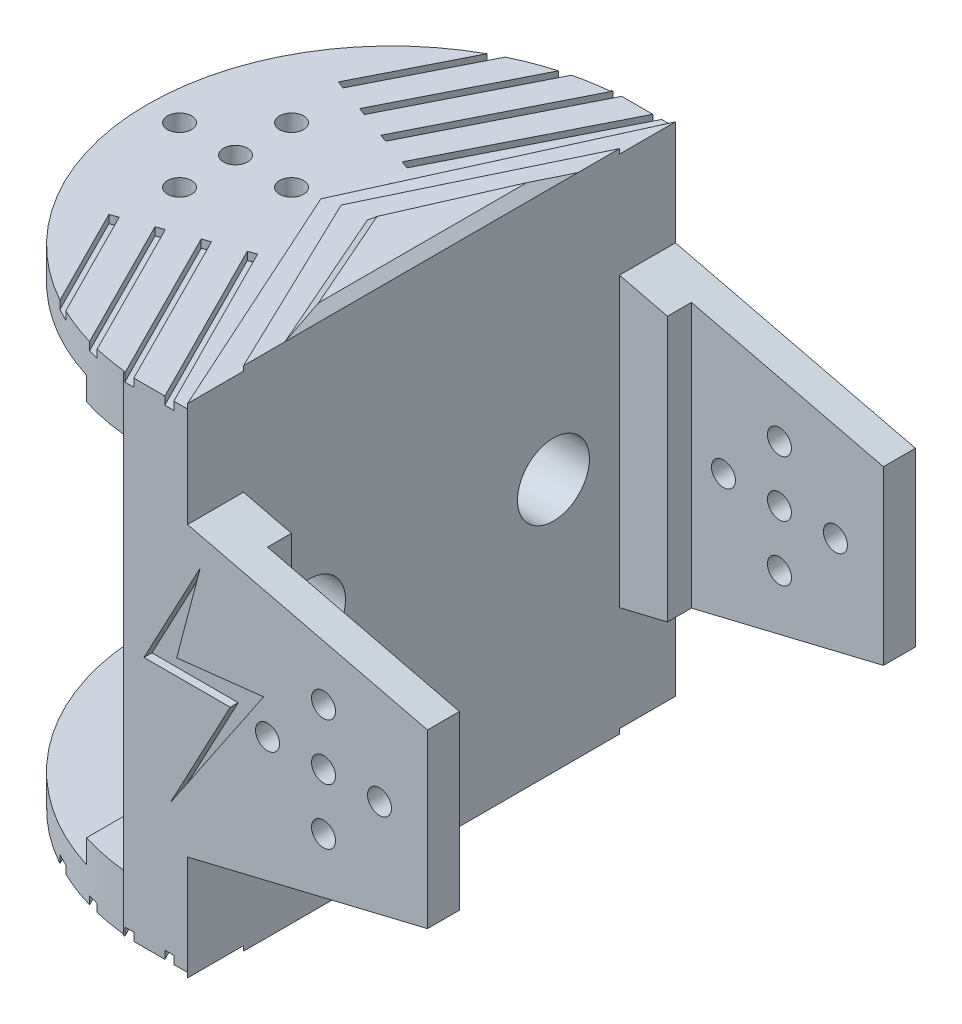
SolidWorks part; units mm, degrees
ref_plane "Front" through (0, 0, 0) normal (0, 0, 1) x (1, 0, 0)
ref_plane "Top" through (0, 0, 0) normal (0, 1, 0) x (1, 0, 0)
ref_plane "Right" through (0, 0, 0) normal (1, 0, 0) x (0, 0, -1)
sketch "草图1" plane through (0, 0, 0) normal (0, 1, 0) x (1, 0, 0)
  line L0 (50.6168, 0) -> (43.6168, 0) construction
  line L1 (43.6168, -30.5) -> (50.6168, -30.5)
  line L3 (43.6168, 30.5) -> (50.6168, 30.5)
  line L4 (50.6168, -30.5) -> (50.6168, 30.5)
  line L5 (-50.6168, -30.5) -> (50.6168, 30.5) construction
  line L6 (-50.6168, 30.5) -> (50.6168, -30.5) construction
  arc A1 (43.6168, 30.5) -> (43.6168, -30.5) centre (43.6168, 0) ccw
  point P0 (0, 0)
extrude "凸台-拉伸1" add sketch "草图1" along normal blind 61
sketch "草图2" plane through (0, 0, 30.5) normal (0, 0, 1) x (1, 0, 0)
  line L0 (50.6168, 61) -> (50.6168, 57) construction
  line L1 (50.6168, 61) -> (50.6168, 0) construction
  line L2 (50.6168, 57) -> (46.6168, 57) construction
  line L3 (50.6168, 0) -> (50.6168, 4) construction
  line L4 (50.6168, 4) -> (46.6168, 4) construction
  line L5 (46.6168, 57) -> (46.6168, 4)
  line L6 (46.6168, 4) -> (6.6168, 4)
  line L7 (6.6168, 4) -> (6.6168, 57)
  line L8 (6.6168, 57) -> (46.6168, 57)
extrude "切除-拉伸1" cut sketch "草图2" against normal blind 61
sketch "草图3" plane through (0, 61, 0) normal (0, 1, 0) x (1, 0, 0)
  circle A1 centre (24.1168, 0) radius 4
extrude "切除-拉伸2" cut sketch "草图3" against normal blind 61
sketch "草图6" plane through (46.6168, 0, 0) normal (-1, 0, 0) x (0, 0, 1)
  line L0 (-30.5, 61) -> (-30.5, 0)
  line L1 (-30.5, 0) -> (30.5, 0)
  line L2 (30.5, 0) -> (30.5, 61)
  line L3 (30.5, 61) -> (-30.5, 61)
extrude "凸台-拉伸3" add sketch "草图6" along normal blind 6
sketch "草图7" plane through (0, 57, 0) normal (0, -1, 0) x (1, 0, 0)
  line L0 (40.6168, 30.3521) -> (40.6168, -30.3521)
  arc A0 (40.6168, 30.3521) -> (40.6168, -30.3521) centre (43.6168, 0) ccw
extrude "凸台-拉伸4" add sketch "草图7" along normal blind 6
sketch "草图8" plane through (0, 51, 0) normal (0, -1, 0) x (1, 0, 0)
  line L0 (40.6168, -30.3521) -> (34.6168, -30.3521) construction
  line L1 (9.6904, -10) -> (9.6904, 10)
  line L2 (34.6168, -30.3521) -> (24.1168, -25.2271)
  line L4 (24.1168, -25.2271) -> (9.6904, -10)
  line L6 (24.1168, 30.2691) -> (9.6904, 10)
  line L7 (34.6168, -30.3521) -> (34.6168, 33.6388)
  line L8 (34.6168, 33.6388) -> (24.1168, 30.2691)
extrude "切除-拉伸4" cut sketch "草图8" against normal blind 6
sketch "草图21" plane through (0, 61, 0) normal (0, 1, 0) x (1, 0, 0)
  circle A0 centre (24.1168, 0) radius 4
  circle A1 centre (24.1168, 0) radius 1.5
extrude "凸台-拉伸10" add sketch "草图21" against normal blind 4
sketch "草图22" plane through (0, 61, 0) normal (0, 1, 0) x (1, 0, 0)
  line L0 (24.1168, 0) -> (31.1168, 0) construction
  circle A0 centre (31.1168, 0) radius 1.5
  circle A1 centre (24.1168, -7) radius 1.5
  circle A2 centre (17.1168, 0) radius 1.5
  circle A3 centre (24.1168, 7) radius 1.5
  point P14 (24.1168, 0)
  dimension "D1" = 4
extrude "切除-拉伸11" cut sketch "草图22" against normal blind 4
sketch "草图23" plane through (50.6168, 0, 0) normal (1, 0, 0) x (0, 0, -1)
  line L0 (-30.5, 61) -> (-30.5, 0)
  line L1 (-30.5, 0) -> (30.5, 0)
  line L2 (30.5, 0) -> (30.5, 61)
  line L3 (30.5, 61) -> (-30.5, 61)
extrude "切除-拉伸12" cut sketch "草图23" against normal blind 2
sketch "草图24" plane through (0, 0, 30.5) normal (0, 0, 1) x (1, 0, 0)
  line L0 (40.6168, 51) -> (40.6168, 54.1)
  line L1 (40.6168, 0) -> (40.6168, 61) construction
  line L2 (40.6168, 54.1) -> (21.6591, 54.1)
  line L3 (21.6591, 54.1) -> (21.6591, 51)
  line L4 (21.6591, 51) -> (40.6168, 51)
  line L5 (40.6168, 30.5) -> (24.5889, 30.5) construction
extrude "切除-拉伸13" cut sketch "草图24" against normal blind 103 and the other way blind 38
ref_plane "基准面1" through (0, 30.5, 0) normal (0, -1, 0) x (-1, 0, 0)
mirror "镜向1" about plane through (0, 30.5, 0) normal (0, -1, 0) of "切除-拉伸4", "凸台-拉伸4", "切除-拉伸11", "切除-拉伸13"
sketch "草图25" plane through (0, 0, 0) normal (0, -1, 0) x (1, 0, 0)
  circle A0 centre (24.1168, 0) radius 4
  circle A1 centre (24.1168, 0) radius 1.5
extrude "凸台-拉伸11" add sketch "草图25" against normal blind 4
sketch "草图26" plane through (0, 0, 30.5) normal (0, 0, 1) x (1, 0, 0)
  line L0 (48.6168, 12.5) -> (48.6168, 48.5)
  line L1 (48.6168, 61) -> (48.6168, 0) construction
  line L2 (48.6168, 30.5) -> (78.6168, 30.5) construction
  line L3 (78.6168, 19.7437) -> (78.6168, 41.2563)
  line L4 (48.6168, 48.5) -> (78.6168, 41.2563)
  line L5 (48.6168, 12.5) -> (78.6168, 19.7437)
  line L6 (48.6168, 30.5) -> (65.6168, 30.5) construction
  line L7 (65.6168, 30.5) -> (65.6168, 37.5)
  circle A0 centre (65.6168, 30.5) radius 1.5
  circle A1 centre (65.6168, 37.5) radius 1.5
  circle A2 centre (72.6168, 30.5) radius 1.5
  circle A3 centre (65.6168, 23.5) radius 1.5
  circle A4 centre (58.6168, 30.5) radius 1.5
  point P21 (65.6168, 30.5)
ref_plane "基准面2" through (0, 0, 0) normal (0, 0, 1) x (1, 0, 0)
extrude "凸台-拉伸12" add sketch "草图26" against normal blind 7
sketch "草图27" plane through (0, 0, 23.5) normal (0, 0, -1) x (-1, 0, 0)
  line L0 (-48.6168, 48.5) -> (-54.6168, 48.5) construction
  line L1 (-65.6168, 49.1559) -> (-88.6288, 40.6)
  line L2 (-88.6288, 40.6) -> (-88.6288, 5.4717)
  line L3 (-88.6288, 5.4717) -> (-65.6168, 5.4717)
  line L4 (-55.5168, 53.0968) -> (-54.6168, 48.5)
  line L6 (-55.5168, 53.0968) -> (-65.6168, 49.1559)
  line L8 (-55.5168, 5.4717) -> (-65.6168, 5.4717)
  line L9 (-54.6168, 48.5) -> (-54.6168, 7.907)
  line L10 (-54.6168, 7.907) -> (-55.5168, 5.4717)
extrude "切除-拉伸14" cut sketch "草图27" against normal blind 3
mirror "镜向2" about plane through (0, 0, 0) normal (0, 0, 1) of "切除-拉伸14", "凸台-拉伸12"
sketch "草图30" plane through (48.6168, 0, 0) normal (1, 0, 0) x (0, 0, -1)
  line L0 (0, 61) -> (0, 0) construction
  line L1 (30.5, 61) -> (-30.5, 61) construction
  line L2 (0, 0) -> (-30.5, 30.5) construction
  line L3 (-30.5, 19.7437) -> (-30.5, 41.2563) construction
  line L4 (-30.5, 30.5) -> (0, 30.5) construction
  line L6 (0, 30.5) -> (30.5, 30.5) construction
  line L7 (30.5, 19.7437) -> (30.5, 41.2563) construction
  circle A0 centre (-15.25, 30.5) radius 4.5
  circle A1 centre (15.25, 30.5) radius 4.5
extrude "切除-拉伸15" cut sketch "草图30" against normal blind 46
sketch "草图31" plane through (0, 61, 0) normal (0, 1, 0) x (1, 0, 0)
  line L0 (48.6168, 30.5) -> (34.7866, 0)
  line L1 (34.7866, 0) -> (48.6168, -30.5)
  line L2 (48.6168, 30.5) -> (48.6168, -30.5)
extrude "凸台-拉伸14" add sketch "草图31" along normal blind 0.6
sketch "草图32" plane through (0, 61.6, 0) normal (0, 1, 0) x (1, 0, 0)
  line L0 (48.6168, 23.5) -> (37.3287, 0)
  line L1 (37.3287, 0) -> (48.6168, -23.5)
  line L2 (48.6168, -23.5) -> (48.6168, 23.5)
extrude "凸台-拉伸15" add sketch "草图32" along normal blind 0.6
sketch "草图33" plane through (0, 62.2, 0) normal (0, 1, 0) x (1, 0, 0)
  line L0 (48.6168, 18.3081) -> (40.5926, 0)
  line L1 (48.6168, -23.5) -> (48.6168, 23.5) construction
  line L2 (40.5926, 0) -> (48.6168, 0) construction
  line L3 (48.6168, -18.3081) -> (40.5926, 0)
  line L4 (48.6168, 18.3081) -> (48.6168, -18.3081)
extrude "凸台-拉伸16" add sketch "草图33" along normal blind 1 draft 48
sketch "草图34" plane through (0, 61, 0) normal (0, 1, 0) x (1, 0, 0)
  line L0 (36.2159, 9.33) -> (48.0493, 32.7789)
  line L1 (48.0493, 32.7789) -> (47.1565, 33.2295)
  line L2 (47.1565, 33.2295) -> (35.2718, 9.6788)
  line L3 (27.7872, 12.4437) -> (26.8431, 12.7925)
  line L4 (32.0016, 10.8869) -> (43.0493, 32.7789)
  line L5 (42.1565, 33.2295) -> (31.0575, 11.2356)
  line L6 (23.5729, 14.0006) -> (22.6288, 14.3493)
  line L7 (43.0493, 32.7789) -> (42.1565, 33.2295)
  line L8 (27.7872, 12.4437) -> (38.0493, 32.7789)
  line L9 (37.1565, 33.2295) -> (26.8431, 12.7925)
  line L10 (40.5926, 0) -> (24.1168, 0) construction
  line L11 (38.0493, 32.7789) -> (37.1565, 33.2295)
  line L12 (23.5729, 14.0006) -> (33.0493, 32.7789)
  line L13 (32.1565, 33.2295) -> (22.6288, 14.3493)
  line L14 (32.0016, -10.8869) -> (31.0575, -11.2356)
  line L15 (33.0493, 32.7789) -> (32.1565, 33.2295)
  line L16 (36.2159, -9.33) -> (35.2718, -9.6788)
  line L17 (33.0493, -32.7789) -> (32.1565, -33.2295)
  line L18 (32.1565, -33.2295) -> (22.6288, -14.3493)
  line L19 (23.5729, -14.0006) -> (33.0493, -32.7789)
  line L20 (38.0493, -32.7789) -> (37.1565, -33.2295)
  line L21 (37.1565, -33.2295) -> (26.8431, -12.7925)
  line L22 (27.7872, -12.4437) -> (38.0493, -32.7789)
  line L23 (43.0493, -32.7789) -> (42.1565, -33.2295)
  line L24 (36.2159, 9.33) -> (35.2718, 9.6788)
  line L25 (32.0016, 10.8869) -> (31.0575, 11.2356)
  line L26 (22.1565, 33.2295) -> (8.4742, 6.1165) [skipped]
  line L27 (14.3669, 5.666) -> (28.0493, 32.7789) [skipped]
  line L28 (27.1565, 33.2295) -> (13.4742, 6.1165) [skipped]
  line L29 (28.0493, 32.7789) -> (27.1565, 33.2295) [skipped]
  line L30 (23.0493, 32.7789) -> (22.1565, 33.2295) [skipped]
  line L31 (9.3669, 5.666) -> (23.0493, 32.7789) [skipped]
  line L32 (23.5729, -14.0006) -> (22.6288, -14.3493)
  line L33 (42.1565, -33.2295) -> (31.0575, -11.2356)
  line L34 (32.0016, -10.8869) -> (43.0493, -32.7789)
  line L35 (27.7872, -12.4437) -> (26.8431, -12.7925)
  line L36 (47.1565, -33.2295) -> (35.2718, -9.6788)
  line L37 (48.0493, -32.7789) -> (47.1565, -33.2295)
  line L38 (36.2159, -9.33) -> (48.0493, -32.7789)
  dimension "D1" = 6
extrude "切除-拉伸16" cut sketch "草图34" against normal blind 1
sketch "草图35" plane through (0, 0, 30.5) normal (0, 0, 1) x (1, 0, 0)
  line L0 (50.2152, 44.6018) -> (43.1708, 31.3826)
  line L1 (43.1708, 31.3826) -> (53.9549, 31.3826)
  line L2 (53.9549, 31.3826) -> (46.4303, 17.2624)
  line L3 (50.2152, 44.6018) -> (47.2583, 33.3829)
  line L4 (47.2583, 33.3829) -> (58.1294, 34.6004)
  line L5 (58.1294, 34.6004) -> (46.4303, 17.2624)
extrude "切除-拉伸17" cut sketch "草图35" against normal blind 1
mirror "镜向3" about plane through (0, 0, 0) normal (0, 0, 1) of "切除-拉伸17"
mirror "镜向4" about plane through (0, 30.5, 0) normal (0, -1, 0) of "切除-拉伸16", "凸台-拉伸14", "凸台-拉伸15", "凸台-拉伸16"
sketch "草图36" plane through (0, 0, 0) normal (0, 0, 1) x (1, 0, 0)
  line L0 (24.1168, 57) -> (24.1168, 4) construction
  line L1 (22.6168, 57) -> (25.6168, 57) construction
  line L2 (25.6168, 4) -> (22.6168, 4) construction
  line L3 (24.1168, 30.5) -> (53.0251, 30.5) construction
ref_plane "基准面3" through (24.1168, 0, 0) normal (1, 0, 0) x (0, 0, -1)
sketch "草图37" plane through (24.1168, 0, 0) normal (1, 0, 0) x (0, 0, -1)
  line L0 (0, 30.5) -> (35.0806, 30.5) construction
  line L1 (0, 57) -> (0, 4) construction
